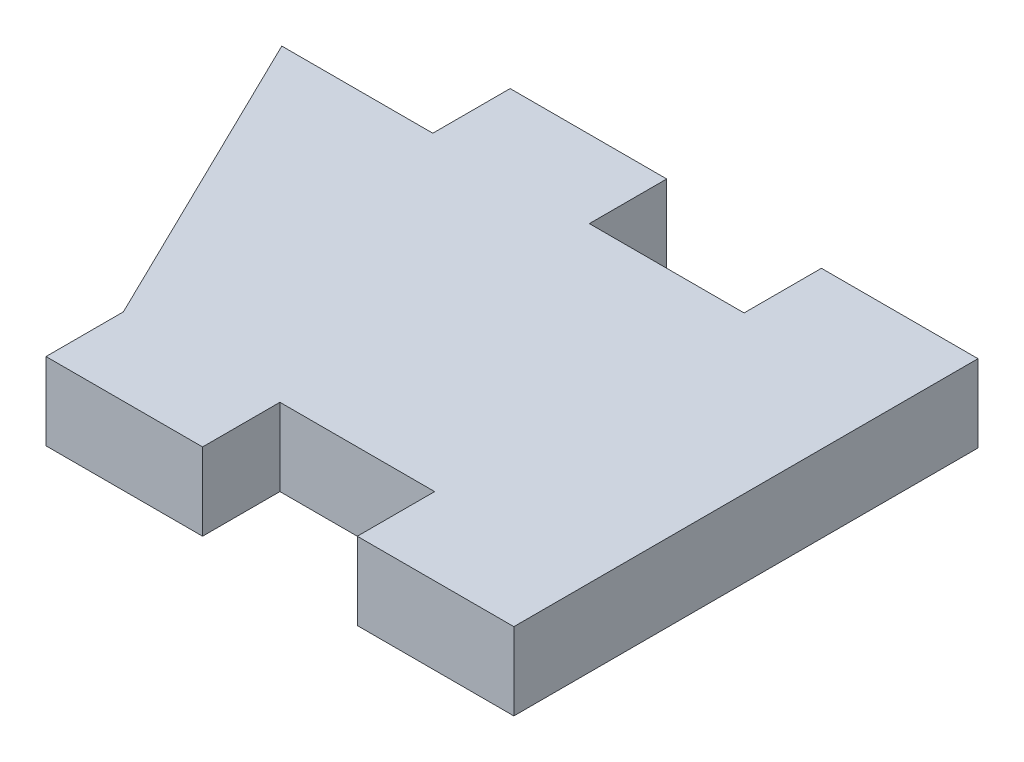
SolidWorks part; units mm, degrees
ref_plane "Front Plane" through (0, 0, 0) normal (0, 0, 1) x (1, 0, 0)
ref_plane "Top Plane" through (0, 0, 0) normal (0, 1, 0) x (1, 0, 0)
ref_plane "Right Plane" through (0, 0, 0) normal (1, 0, 0) x (0, 0, -1)
sketch "Sketch1" plane through (0, 0, 0) normal (0, 1, 0) x (1, 0, 0)
  line L1 (-12.7, 6.35) -> (12.7, 6.35)
  line L2 (-12.7, 6.35) -> (-12.7, -6.35)
  line L3 (-12.7, -6.35) -> (12.7, -6.35)
  line L4 (12.7, 6.35) -> (12.7, -6.35)
  dimension "D1" = 25.4
  dimension "D2" = 12.7
  dimension "D3" = 6.35
  dimension "D4" = 12.7
extrude "Boss-Extrude1" add sketch "Sketch1" along normal blind 3.175
sketch "Sketch2" plane through (0, 0, 6.35) normal (0, 0, 1) x (1, 0, 0)
  line L0 (-12.7, 0) -> (12.7, 0) construction
  line L1 (12.7, 3.175) -> (6.2738, 3.175)
  line L2 (12.7, 3.175) -> (12.7, 0)
  line L3 (12.7, 0) -> (6.2738, 0)
  line L4 (6.2738, 3.175) -> (6.2738, 0)
  line L5 (-12.7, 3.175) -> (12.7, 3.175) construction
  line L6 (-0.0762, 3.175) -> (-6.5024, 3.175)
  line L7 (-0.0762, 3.175) -> (-0.0762, 0)
  line L8 (-0.0762, 0) -> (-6.5024, 0)
  line L9 (-6.5024, 3.175) -> (-6.5024, 0)
  dimension "D1" = 6.4262
  dimension "D2" = 6.4262
  dimension "D3" = 6.35
extrude "Boss-Extrude2" add sketch "Sketch2" along normal blind 3.175
mirror "Mirror1" about plane through (0, 0, 0) normal (0, 0, 1) of "Boss-Extrude2"
sketch "Sketch3" plane through (0, 3.175, 0) normal (0, 1, 0) x (1, 0, 0)
  line L0 (-6.5024, -6.35) -> (-12.7, 6.35)
  line L1 (-12.7, 6.35) -> (-12.7, -6.35)
  line L2 (-12.7, -6.35) -> (-6.5024, -6.35) construction
  line L3 (-12.7, 6.35) -> (-12.7, -6.35) construction
  line L4 (-12.7, -6.35) -> (-6.5024, -6.35)
extrude "Cut-Extrude1" cut sketch "Sketch3" against normal blind 3.175
